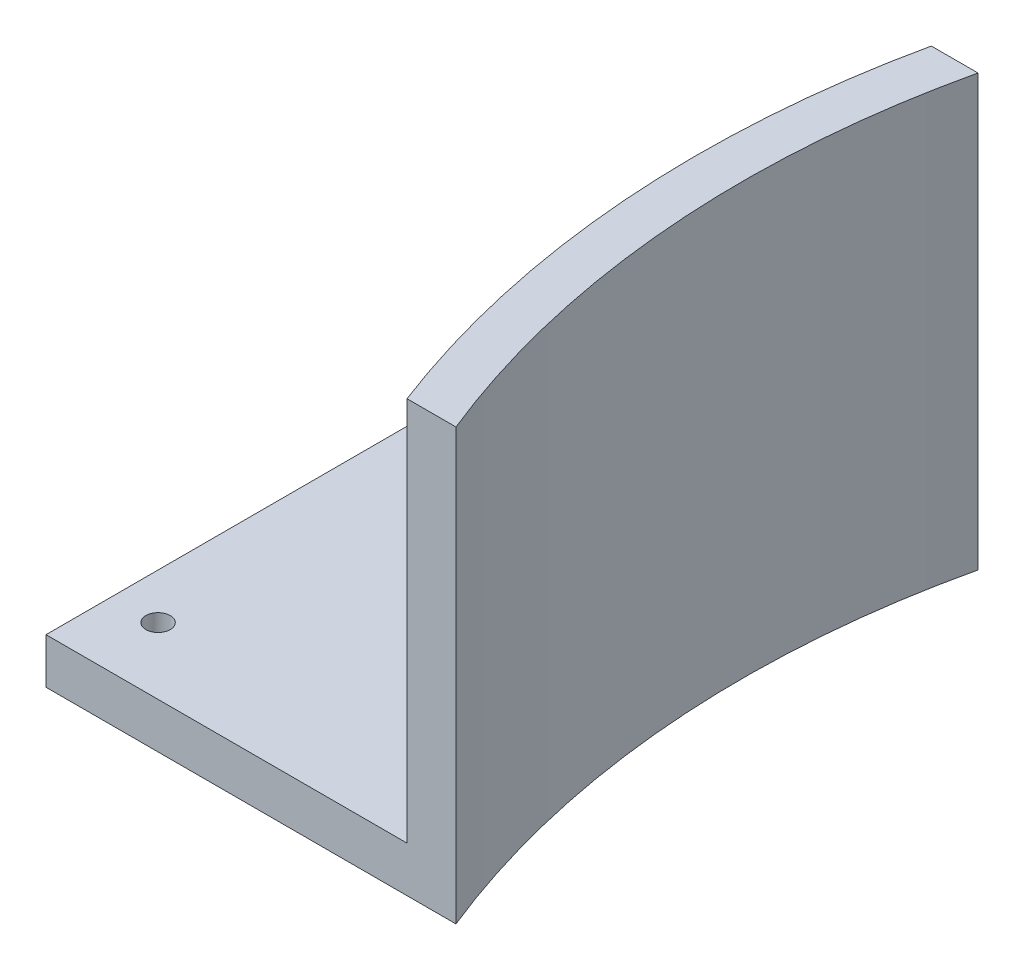
SolidWorks part; units mm, degrees
ref_plane "Front Plane" through (0, 0, 0) normal (0, 0, 1) x (1, 0, 0)
ref_plane "Top Plane" through (0, 0, 0) normal (0, 1, 0) x (1, 0, 0)
ref_plane "Right Plane" through (0, 0, 0) normal (1, 0, 0) x (0, 0, -1)
sketch "Sketch1" plane through (0, 0, 0) normal (0, 1, 0) x (1, 0, 0)
  line L0 (50.8, 79.121) -> (0, 79.121)
  line L1 (0, 79.121) -> (0, 0)
  line L2 (0, 0) -> (57.15, 0)
  arc A1 (50.8, 79.121) -> (57.15, 0) centre (179.5475, 49.6385) ccw
  dimension "D2" = 264.16
  dimension "D1" = 50.8
  dimension "D3" = 79.121
  dimension "D4" = 57.15
extrude "Boss-Extrude1" add sketch "Sketch1" along normal blind 60
sketch "Sketch3" plane through (0, 0, 0) normal (0, 1, 0) x (1, 0, 0)
  line L0 (51.2655, -2.3865) -> (0, 0)
  line L2 (0, 0) -> (0, 79.121)
  line L3 (0, 79.121) -> (44.2935, 79.121)
  line L5 (50.8, 79.121) -> (0, 79.121) construction
  arc A3 (44.6102, 80.5384) -> (51.2655, -2.3865) centre (179.5475, 49.6385) ccw
  arc A4 (44.2935, 79.121) -> (51.2655, -2.3865) centre (179.5475, 49.6385) ccw
  dimension "D1" = 6.35
extrude "Cut-Extrude1" cut sketch "Sketch3" against normal offset from surface (53.65 mm away) 6.35 from surface at 60 up to face at (25.4665, 0, -39.4384) starting at face at (25.4665, 60, -39.4384)
sketch "Sketch4" plane through (0, 6.35, 0) normal (0, 1, 0) x (1, 0, 0)
  line L0 (44.2935, 79.121) -> (0, 79.121) construction
  line L1 (0, 79.121) -> (0, 0) construction
  circle A0 centre (6.35, 72.771) radius 1.7
  circle A1 centre (25.4, 72.771) radius 1.7
  circle A3 centre (6.35, 9.271) radius 1.7
  circle A4 centre (25.4, 9.271) radius 1.7 [skipped]
  dimension "D1" = 3.4
  dimension "D2" = 6.35
  dimension "D3" = 6.35
  dimension "D4" = 2
  dimension "D5" = 2
extrude "Cut-Extrude2" cut sketch "Sketch4" against normal through all
equation "\"tightTol\"= 0.005in"
equation "\"normTol\"= 0.01in"
equation "\"looseTol\"= 0.02in"
equation "\"D3@Sketch1\"=3.125000in-\"normTol\""
equation "\"D1@Sketch4\"=3.4mm"
equation "\"D1@Boss-Extrude1\"=60mm"
